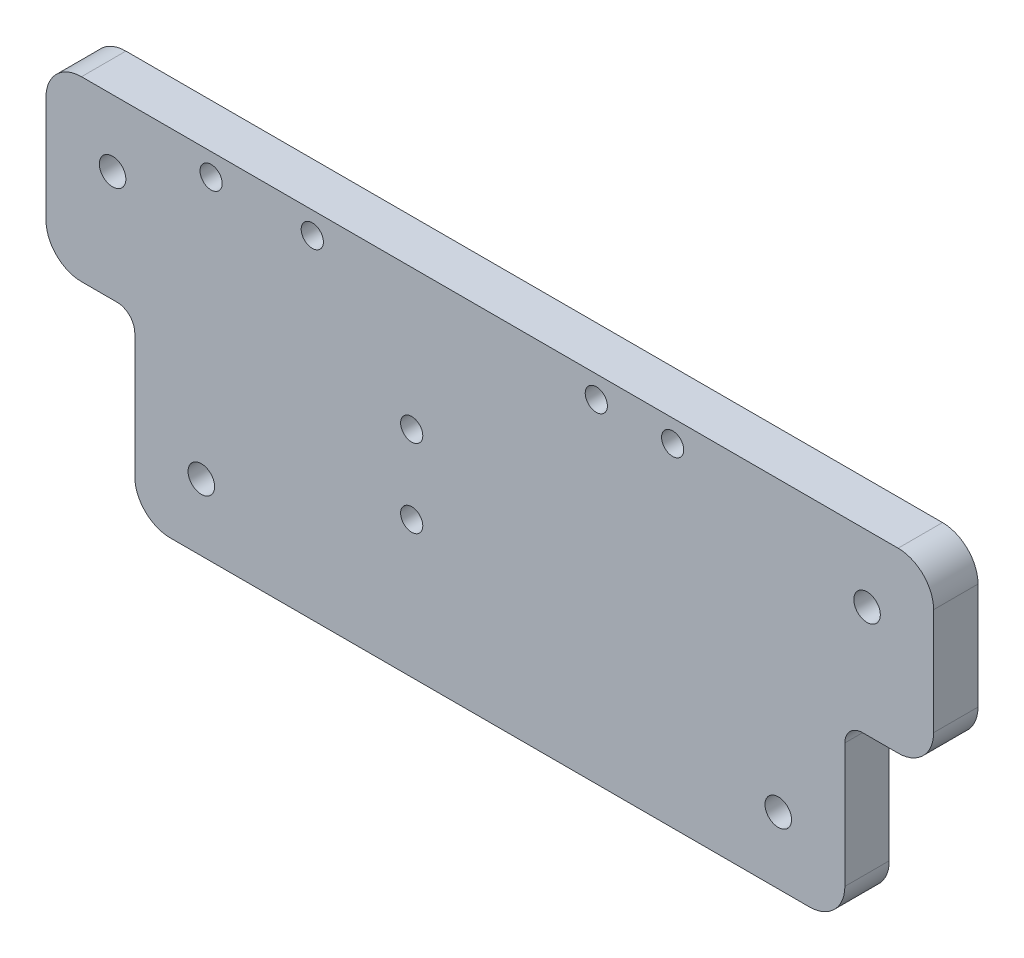
SolidWorks part; units mm, degrees
ref_plane "Front Plane" through (0, 0, 0) normal (0, 0, 1) x (1, 0, 0)
ref_plane "Top Plane" through (0, 0, 0) normal (0, 1, 0) x (1, 0, 0)
ref_plane "Right Plane" through (0, 0, 0) normal (1, 0, 0) x (0, 0, -1)
sketch "Sketch1" plane through (0, 0, 0) normal (0, 0, 1) x (1, 0, 0)
  line L0 (0, 25.4) -> (12.7, 25.4)
  line L1 (0, 0) -> (127, 0)
  line L2 (0, 0) -> (0, 50.8)
  line L3 (0, 50.8) -> (127, 50.8)
  line L4 (127, 0) -> (127, 50.8)
  line L5 (12.7, 25.4) -> (12.7, 0)
  line L6 (127, 25.4) -> (114.3, 25.4)
  line L7 (114.3, 25.4) -> (114.3, 0)
  circle A0 centre (23.622, 47.625) radius 1.5875
  circle A1 centre (38.1, 47.625) radius 1.5875
  circle A2 centre (78.74, 47.625) radius 1.5875
  circle A3 centre (89.662, 47.625) radius 1.5875
  circle A4 centre (52.324, 30.734) radius 1.5875
  circle A5 centre (52.324, 19.558) radius 1.5875
  circle A6 centre (9.525, 41.275) radius 1.8986
  circle A7 centre (22.225, 9.525) radius 1.8986
  circle A8 centre (104.775, 9.525) radius 1.8987
  circle A9 centre (117.475, 41.275) radius 1.8986
  dimension "D6" = 3.175
  dimension "D16" = 3.7973
  dimension "D1" = 127
  dimension "D2" = 50.8
  dimension "D3" = 12.7
  dimension "D4" = 12.7
  dimension "D5" = 25.4
  dimension "D7" = 14.478
  dimension "D8" = 10.922
  dimension "D9" = 3.175
  dimension "D10" = 3.175
  dimension "D11" = 20.066
  dimension "D12" = 11.176
  dimension "D13" = 38.1
  dimension "D14" = 48.26
  dimension "D15" = 52.324
  dimension "D17" = 9.525
  dimension "D18" = 9.525
  dimension "D19" = 9.525
  dimension "D20" = 9.525
  dimension "D21" = 9.525
  dimension "D22" = 9.525
  dimension "D23" = 9.525
  dimension "D24" = 9.525
extrude "Boss-Extrude1" add sketch "Sketch1" along normal blind 6.35 contours L7 L6 L4 L3 L2 L0 L5 L1 A9 A8 A7 A6 A5 A4 A3 A2 A1 A0
fillet "Fillet1" radius 5.08 6 edges at (0, 25.4, 3.175) (12.7, 0, 3.175) (114.3, 0, 3.175) (127, 25.4, 3.175) (127, 50.8, 3.175) (0, 50.8, 3.175)
fillet "Fillet2" radius 2.54 2 edges at (114.3, 25.4, 3.175) (12.7, 25.4, 3.175)
